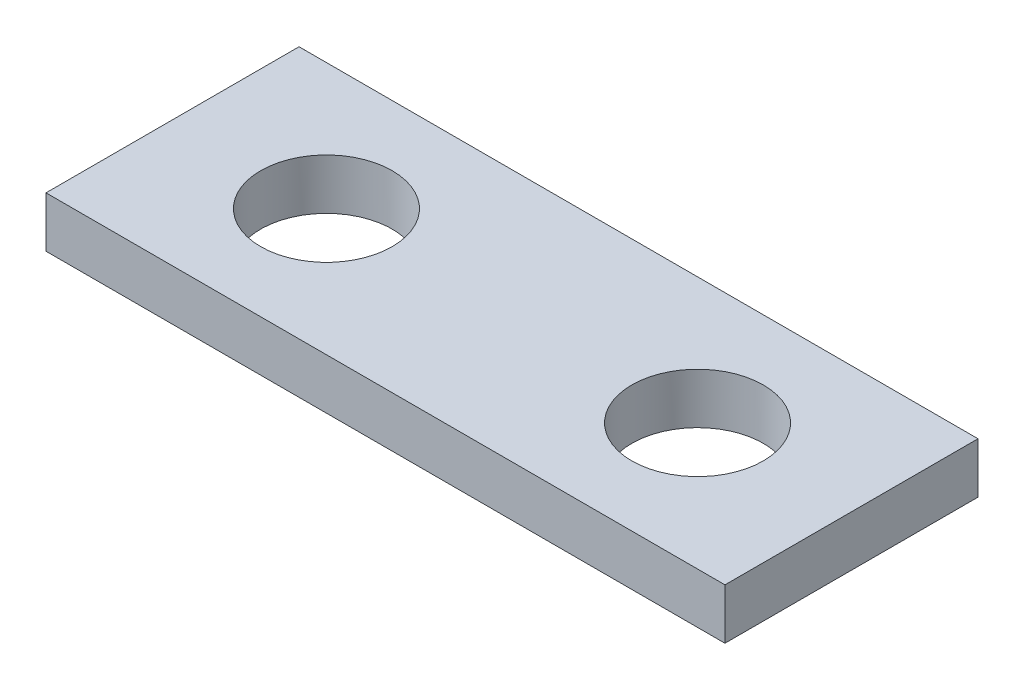
SolidWorks part; units mm, degrees
ref_plane "Front Plane" through (0, 0, 0) normal (0, 0, 1) x (1, 0, 0)
ref_plane "Top Plane" through (0, 0, 0) normal (0, 1, 0) x (1, 0, 0)
ref_plane "Right Plane" through (0, 0, 0) normal (1, 0, 0) x (0, 0, -1)
sketch "Sketch1" plane through (0, 0, 0) normal (0, 1, 0) x (1, 0, 0)
  line L1 (-20.125, -7.5) -> (20.125, -7.5)
  line L2 (-20.125, -7.5) -> (-20.125, 7.5)
  line L3 (-20.125, 7.5) -> (20.125, 7.5)
  line L4 (20.125, -7.5) -> (20.125, 7.5)
  line L5 (-20.125, -7.5) -> (20.125, 7.5) construction
  line L6 (-20.125, 7.5) -> (20.125, -7.5) construction
  point P0 (0, 0)
  dimension "D1" = 40.25
  dimension "D2" = 15
extrude "Boss-Extrude1" add sketch "Sketch1" along normal blind 3
sketch "Sketch2" plane through (0, 3, 0) normal (0, 1, 0) x (1, 0, 0)
  circle A0 centre (-11, 0) radius 3.9
  dimension "D2" = 7.8
  dimension "D1" = 11
extrude "Cut-Extrude1" cut sketch "Sketch2" against normal through all both and the other way through all
mirror "Mirror1" about plane through (0, 0, 0) normal (1, 0, 0) of "Cut-Extrude1"
